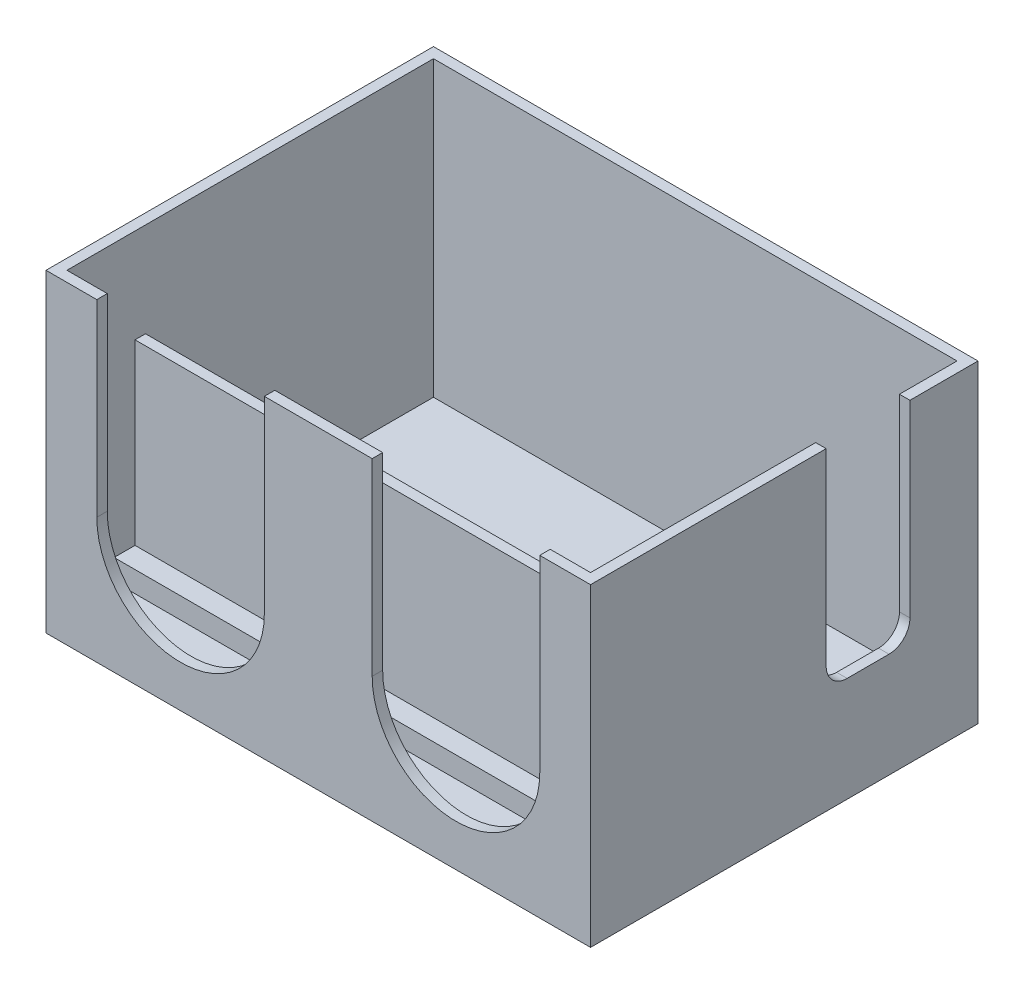
SolidWorks part; units mm, degrees
ref_plane "Front Plane" through (0, 0, 0) normal (0, 0, 1) x (1, 0, 0)
ref_plane "Top Plane" through (0, 0, 0) normal (0, 1, 0) x (1, 0, 0)
ref_plane "Right Plane" through (0, 0, 0) normal (1, 0, 0) x (0, 0, -1)
sketch "Sketch1" plane through (0, 0, 0) normal (0, 1, 0) x (1, 0, 0)
  line L1 (0, 0) -> (52, 0)
  line L2 (0, 0) -> (0, 37)
  line L3 (0, 37) -> (52, 37)
  line L4 (52, 0) -> (52, 37)
  line L5 (1, 1) -> (51, 1)
  line L6 (1, 1) -> (1, 36)
  line L7 (1, 36) -> (51, 36)
  line L8 (51, 1) -> (51, 36)
  point P9 (52, 18.5)
  point P10 (51, 18.5)
  point P11 (26, 1)
  point P12 (26, 0)
  dimension "D1" = 37
  dimension "D2" = 52
  dimension "D3" = 50
  dimension "D4" = 35
extrude "Boss-Extrude1" add sketch "Sketch1" along normal blind 30
sketch "Sketch2" plane through (0, 0, 0) normal (0, 1, 0) x (1, 0, 0)
  line L1 (0, 37) -> (52, 37)
  line L2 (0, 37) -> (0, 0)
  line L3 (0, 0) -> (52, 0)
  line L4 (52, 37) -> (52, 0)
extrude "Boss-Extrude2" add sketch "Sketch2" along normal blind 2
ref_plane "Plane1" through (0, 0, 0) normal (0, 0, 1) x (1, 0, 0)
sketch "Sketch3" plane through (0, 0, 0) normal (0, 0, 1) x (1, 0, 0)
  line L0 (0, 0) -> (52, 0) construction
  line L1 (12.85, 12) -> (39.15, 12) construction
  line L2 (4.85, 12) -> (4.85, 30)
  line L3 (0, 30) -> (52, 30) construction
  line L4 (20.85, 12) -> (20.85, 30)
  line L5 (20.85, 30) -> (4.85, 30)
  line L6 (31.15, 12) -> (31.15, 30)
  line L7 (31.15, 30) -> (47.15, 30)
  line L8 (47.15, 30) -> (47.15, 12)
  arc A0 (4.85, 12) -> (20.85, 12) centre (12.85, 12) ccw
  arc A1 (31.15, 12) -> (47.15, 12) centre (39.15, 12) ccw
  point P4 (26, 0)
  point P7 (26, 12)
  dimension "D1" = 16
  dimension "D2" = 12
  dimension "D3" = 26.3
extrude "Cut-Extrude1" cut sketch "Sketch3" against normal blind 2
ref_plane "Plane2" through (0, 2, 0) normal (0, 1, 0) x (1, 0, 0)
sketch "Sketch4" plane through (0, 2, 0) normal (0, 1, 0) x (1, 0, 0)
  line L0 (1, 36) -> (1, 1) construction
  line L1 (1, 5.5) -> (51, 5.5)
  line L2 (1, 5.5) -> (1, 7.5)
  line L3 (1, 7.5) -> (51, 7.5)
  line L4 (51, 5.5) -> (51, 7.5)
  line L5 (51, 1) -> (51, 36) construction
  line L6 (1, 1) -> (51, 1) construction
  line L8 (51, 13.5) -> (1, 13.5)
  line L9 (51, 13.5) -> (51, 15.5)
  line L10 (51, 15.5) -> (1, 15.5)
  line L11 (1, 13.5) -> (1, 15.5)
  line L12 (51, 17.25) -> (1, 17.25)
  line L13 (51, 17.25) -> (51, 19.25)
  line L14 (51, 19.25) -> (1, 19.25)
  line L15 (1, 17.25) -> (1, 19.25)
  dimension "D1" = 2
  dimension "D2" = 4.5
  dimension "D3" = 2
  dimension "D4" = 6
  dimension "D5" = 2
  dimension "D6" = 1.75
extrude "Boss-Extrude3" add sketch "Sketch4" along normal blind 2
ref_plane "Plane3" through (52, 0, 0) normal (1, 0, 0) x (0, 0, -1)
sketch "Sketch5" plane through (52, 0, 0) normal (1, 0, 0) x (0, 0, -1)
  line L0 (0, 30) -> (37, 30) construction
  line L1 (30.5, 30) -> (22.5, 30)
  line L2 (30.5, 30) -> (30.5, 12)
  line L3 (28.5, 10) -> (24.5, 10)
  line L4 (22.5, 30) -> (22.5, 12)
  arc A0 (24.5, 10) -> (22.5, 12) centre (24.5, 12) cw
  arc A1 (28.5, 10) -> (30.5, 12) centre (28.5, 12) ccw
  point P9 (22.5, 10)
  point P12 (30.5, 10)
  dimension "D4" = 2
  dimension "D1" = 6.5
  dimension "D2" = 8
  dimension "D3" = 20
extrude "Cut-Extrude2" cut sketch "Sketch5" against normal up to next
sketch "Sketch7" plane through (0, 2, 0) normal (0, 1, 0) x (1, 0, 0)
  line L0 (1, 13.5) -> (1, 7.5) construction
  line L1 (51, 7.5) -> (1, 7.5)
  line L2 (51, 7.5) -> (51, 8.5)
  line L3 (51, 8.5) -> (1, 8.5)
  line L4 (1, 7.5) -> (1, 8.5)
  dimension "D1" = 1
extrude "Boss-Extrude4" add sketch "Sketch7" along normal blind 19
